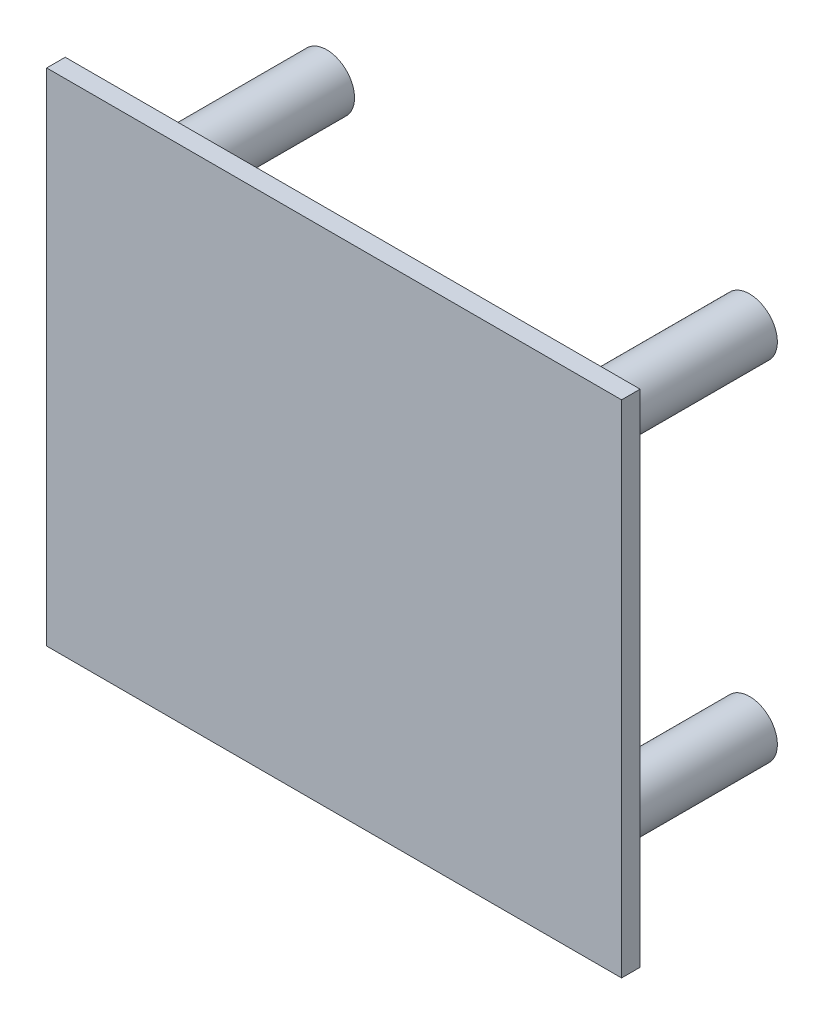
SolidWorks part; units mm, degrees
ref_plane "Front Plane" through (0, 0, 0) normal (0, 0, 1) x (1, 0, 0)
ref_plane "Top Plane" through (0, 0, 0) normal (0, 1, 0) x (1, 0, 0)
ref_plane "Right Plane" through (0, 0, 0) normal (1, 0, 0) x (0, 0, -1)
sketch "Sketch1" plane through (0, 0, 0) normal (0, 0, 1) x (1, 0, 0)
  line L1 (-15.5, -13.5) -> (15.5, -13.5)
  line L2 (-15.5, -13.5) -> (-15.5, 13.5)
  line L3 (-15.5, 13.5) -> (15.5, 13.5)
  line L4 (15.5, -13.5) -> (15.5, 13.5)
  line L5 (-15.5, -13.5) -> (15.5, 13.5) construction
  line L6 (-15.5, 13.5) -> (15.5, -13.5) construction
  point P0 (0, 0)
  dimension "D1" = 31
  dimension "D2" = 27
extrude "Boss-Extrude1" add sketch "Sketch1" along normal blind 1
sketch "Sketch2" plane through (0, 0, 0) normal (0, 0, -1) x (-1, 0, 0)
  line L0 (15.5, -13.5) -> (-15.5, -13.5) construction
  line L1 (-15.5, -13.5) -> (-15.5, 13.5) construction
  circle A0 centre (-11.4, -9.4) radius 1.5
  dimension "D1" = 3
  dimension "D2" = 4.1
  dimension "D3" = 4.1
extrude "Boss-Extrude2" add sketch "Sketch2" along normal blind 10
mirror "Mirror1" about plane through (0, 0, 0) normal (0, 1, 0) of "Boss-Extrude2"
mirror "Mirror2" about plane through (0, 0, 0) normal (1, 0, 0) of "Mirror1", "Boss-Extrude2"
